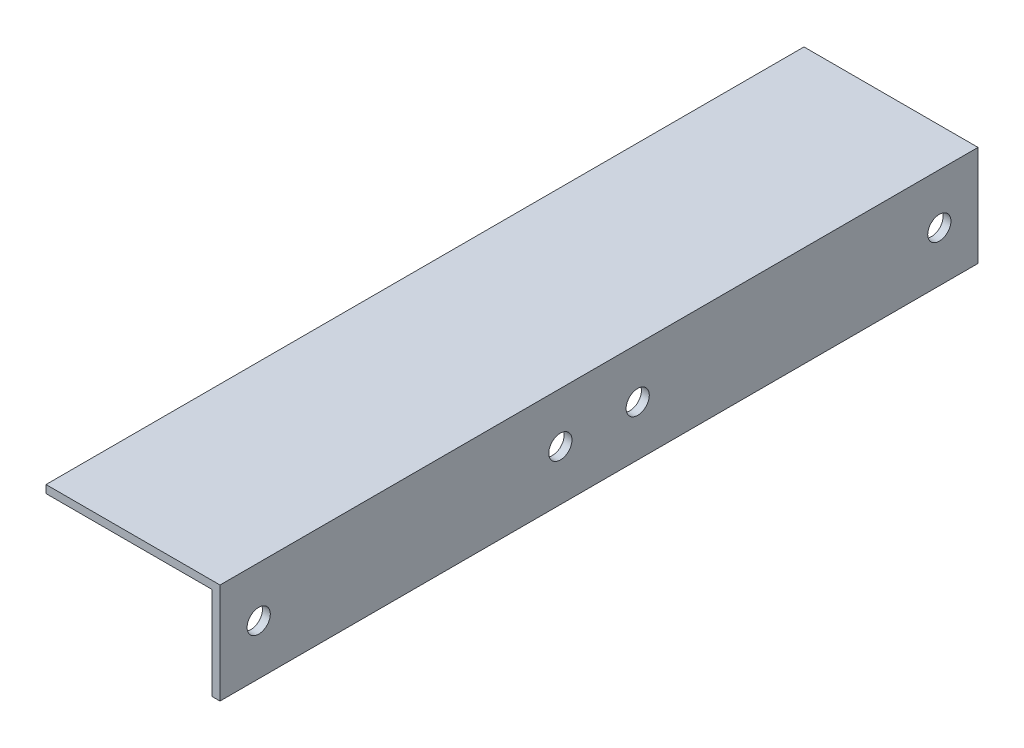
SolidWorks part; units mm, degrees
ref_plane "Front Plane" through (0, 0, 0) normal (0, 0, 1) x (1, 0, 0)
ref_plane "Top Plane" through (0, 0, 0) normal (0, 1, 0) x (1, 0, 0)
ref_plane "Right Plane" through (0, 0, 0) normal (1, 0, 0) x (0, 0, -1)
sketch "Sketch1" plane through (0, 0, 0) normal (0, 0, 1) x (1, 0, 0)
  line L0 (0, 0) -> (-22.5, 0)
  line L1 (0, 0) -> (0, -13)
  line L2 (-1.016, -1.016) -> (-1.016, -13)
  line L3 (-1.016, -1.016) -> (-22.5, -1.016)
  line L4 (-22.5, 0) -> (-22.5, -1.016)
  line L5 (-22.5, -1.016) -> (-22.7455, -1.0229)
  line L6 (-1.016, -13) -> (0, -13)
  dimension "D1" = 22.5
  dimension "D2" = 13
  dimension "D3" = 1.016
extrude "Boss-Extrude1" add sketch "Sketch1" along normal blind 98 contours L4 L0 L1 L6 L2 L3
sketch "Sketch2" plane through (0, 0, 0) normal (1, 0, 0) x (0, 0, -1)
  line L0 (-98, -6.5) -> (0, -6.5) construction
  line L1 (-98, 0) -> (-98, -13) construction
  line L2 (0, 0) -> (0, -13) construction
  line L3 (-49, 0) -> (-49, -13) construction
  line L4 (-98, 0) -> (0, 0) construction
  line L5 (-98, -13) -> (0, -13) construction
  line L6 (-49, 0) -> (-98, 0) construction
  line L7 (-73.5, 0) -> (-73.5, -13) construction
  circle A0 centre (-93, -6.5) radius 1.5
  circle A1 centre (-54, -6.5) radius 1.5
  circle A2 centre (-44, -6.5) radius 1.5
  circle A3 centre (-5, -6.5) radius 1.5
  dimension "D1" = 39
  dimension "D2" = 3
extrude "Cut-Extrude1" cut sketch "Sketch2" against normal blind 40
